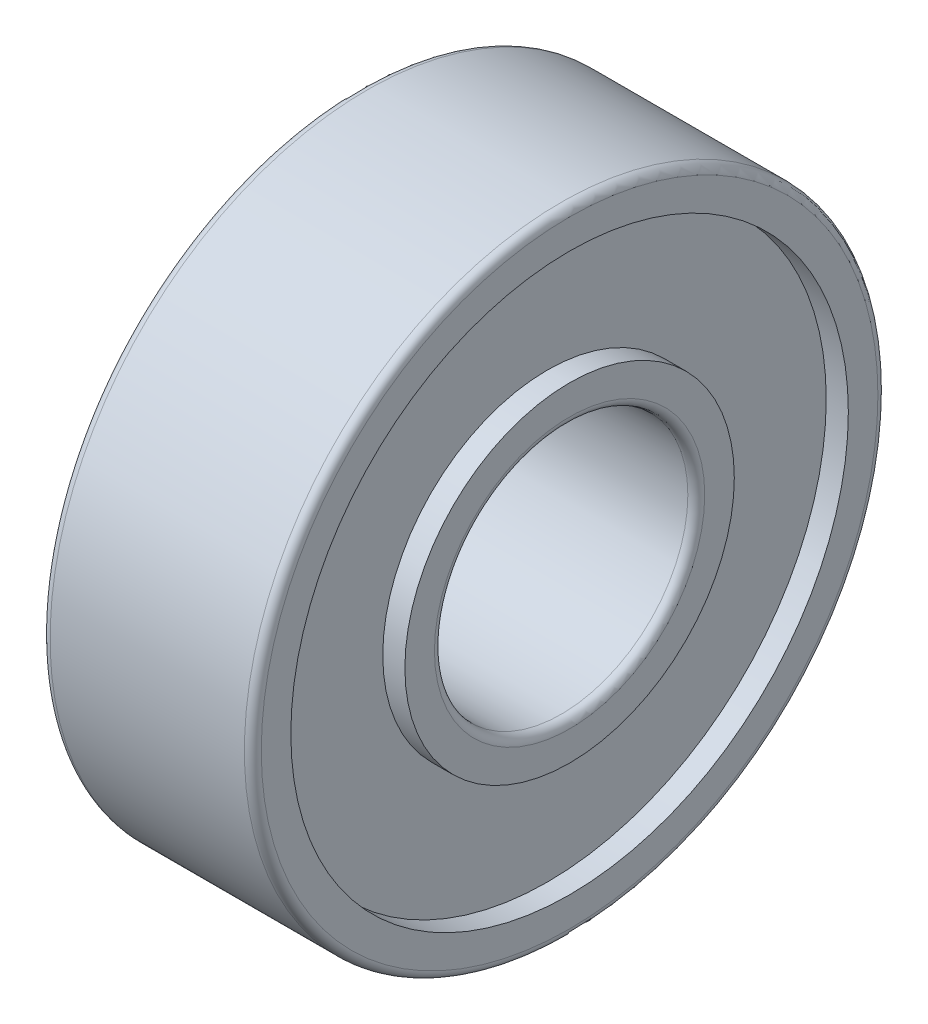
SolidWorks part; units mm, degrees
material "201 Annealed Stainless Steel (SS)"
ref_plane "Front Plane" through (0, 0, 0) normal (0, 0, 1) x (1, 0, 0)
ref_plane "Top Plane" through (0, 0, 0) normal (0, 1, 0) x (1, 0, 0)
ref_plane "Right Plane" through (0, 0, 0) normal (1, 0, 0) x (0, 0, -1)
sketch "Sketch1" plane through (0, 0, 0) normal (0, 0, 1) x (1, 0, 0)
  line L0 (0, 3.9) -> (0, 3.2)
  line L1 (0.2, 3) -> (4.8, 3)
  line L2 (5, 3.2) -> (5, 3.9)
  line L3 (5, 3.9) -> (4.4765, 3.9)
  line L4 (4.4765, 3.9) -> (4.4765, 6.6)
  line L5 (4.4765, 6.6) -> (5, 6.6)
  line L6 (5, 6.6) -> (5, 7.3)
  line L7 (4.8, 7.5) -> (0.2, 7.5)
  line L8 (0, 7.3) -> (0, 6.6)
  line L9 (0, 6.6) -> (0.5235, 6.6)
  line L10 (0.5235, 6.6) -> (0.5235, 3.9)
  line L11 (0.5235, 3.9) -> (0, 3.9)
  line L12 (-0.0013, 0) -> (5.0013, 0) construction
  arc A0 (0, 3.2) -> (0.2, 3) centre (0.2, 3.2) ccw
  arc A1 (4.8, 3) -> (5, 3.2) centre (4.8, 3.2) ccw
  arc A2 (5, 7.3) -> (4.8, 7.5) centre (4.8, 7.3) ccw
  arc A3 (0.2, 7.5) -> (0, 7.3) centre (0.2, 7.3) ccw
revolve "Revolve1" add sketch "Sketch1" angle 360 about L12
